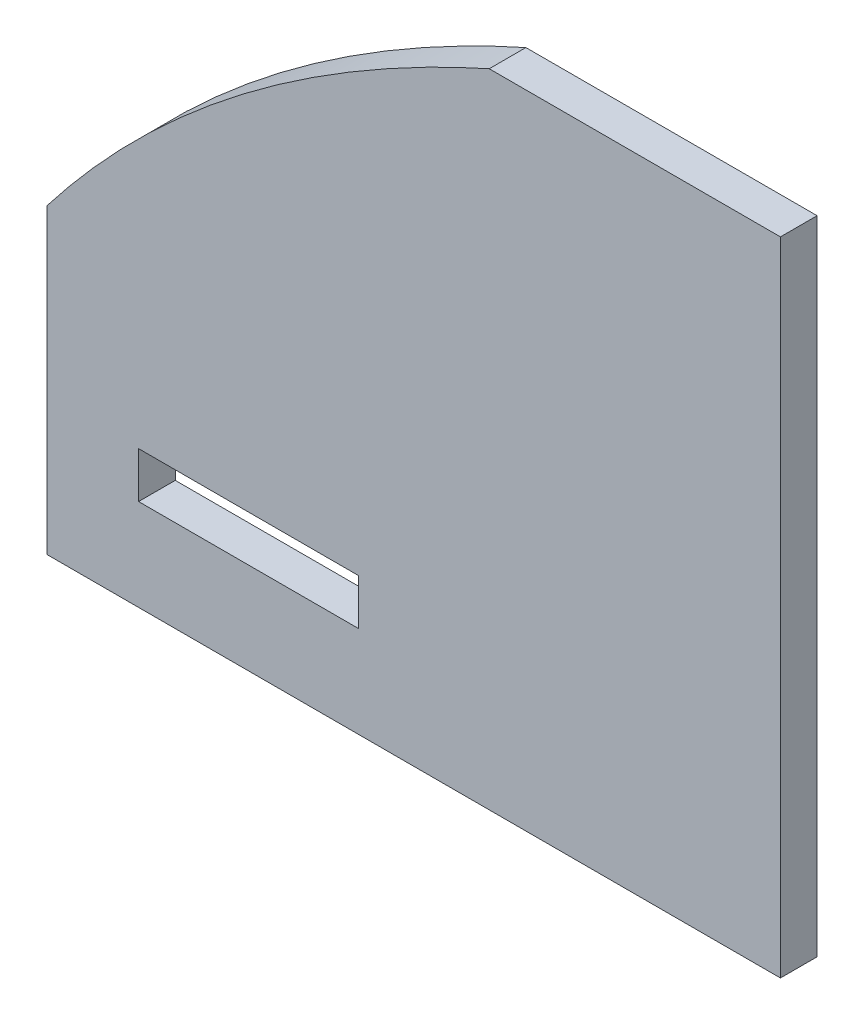
SolidWorks part; units mm, degrees
ref_plane "Plan de face" through (0, 0, 0) normal (0, 0, 1) x (1, 0, 0)
ref_plane "Plan de dessus" through (0, 0, 0) normal (0, 1, 0) x (1, 0, 0)
ref_plane "Plan de droite" through (0, 0, 0) normal (1, 0, 0) x (0, 0, -1)
sketch "Esquisse1" plane through (0, 0, 0) normal (0, 0, 1) x (1, 0, 0)
  line L1 (-20, -17.5) -> (20, -17.5)
  line L2 (-20, -17.5) -> (-20, 17.5)
  line L3 (-20, 17.5) -> (20, 17.5)
  line L4 (20, -17.5) -> (20, 17.5)
  line L5 (-20, -17.5) -> (20, 17.5) construction
  line L6 (-20, 17.5) -> (20, -17.5) construction
  line L7 (-15, -12.5) -> (-3, -12.5)
  line L8 (-15, -12.5) -> (-15, -10)
  line L9 (-15, -10) -> (-3, -10)
  line L10 (-3, -12.5) -> (-3, -10)
  point P0 (0, 0)
  dimension "D1" = 40
  dimension "D2" = 35
  dimension "D3" = 2.5
  dimension "D4" = 12
  dimension "D5" = 5
  dimension "D6" = 5
extrude "Boss.-Extru.1" add sketch "Esquisse1" along normal blind 2
sketch "Esquisse2" plane through (0, 0, 2) normal (0, 0, 1) x (1, 0, 0)
  line L0 (20, 17.5) -> (-20, 17.5) construction
  line L1 (-20, 17.5) -> (-20, -17.5) construction
  line L2 (-28.9974, -17.6239) -> (-30.2654, 23.8682)
  line L3 (-30.2654, 23.8682) -> (4.12, 17.5)
  spline S0 degree 2 poles (4.12, 17.5) (-20.2355, 6.5894) (-28.9974, -17.6239) knots 0 0 0 1 1 1
  point P0 (4.12, 17.5)
  point P1 (-20, -1.03)
  dimension "D1" = 15.88
  dimension "D2" = 16.47
extrude "Enlèv. mat.-Extru.1" cut sketch "Esquisse2" against normal blind 10
